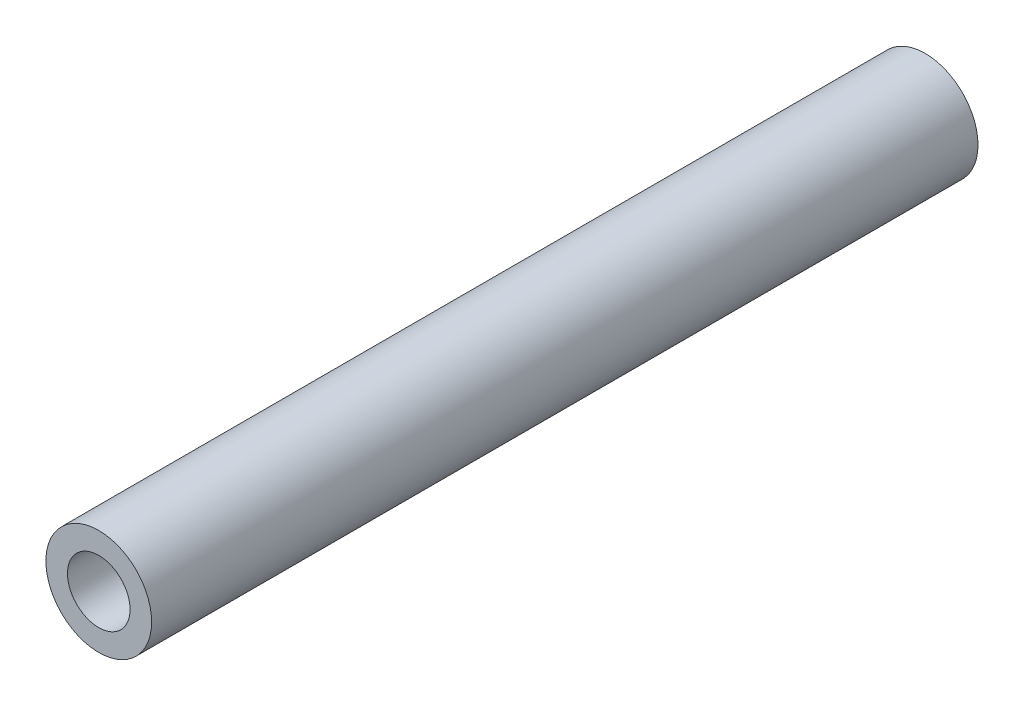
SolidWorks part; units mm, degrees
ref_plane "Plan de face" through (0, 0, 0) normal (0, 0, 1) x (1, 0, 0)
ref_plane "Plan de dessus" through (0, 0, 0) normal (0, 1, 0) x (1, 0, 0)
ref_plane "Plan de droite" through (0, 0, 0) normal (1, 0, 0) x (0, 0, -1)
sketch "Esquisse1" plane through (0, 0, 0) normal (0, 0, 1) x (1, 0, 0)
  circle A0 centre (0, 0) radius 1.45
  circle A1 centre (0, 0) radius 2.45
extrude "Boss.-Extru.1" add sketch "Esquisse1" along normal blind 38.3
